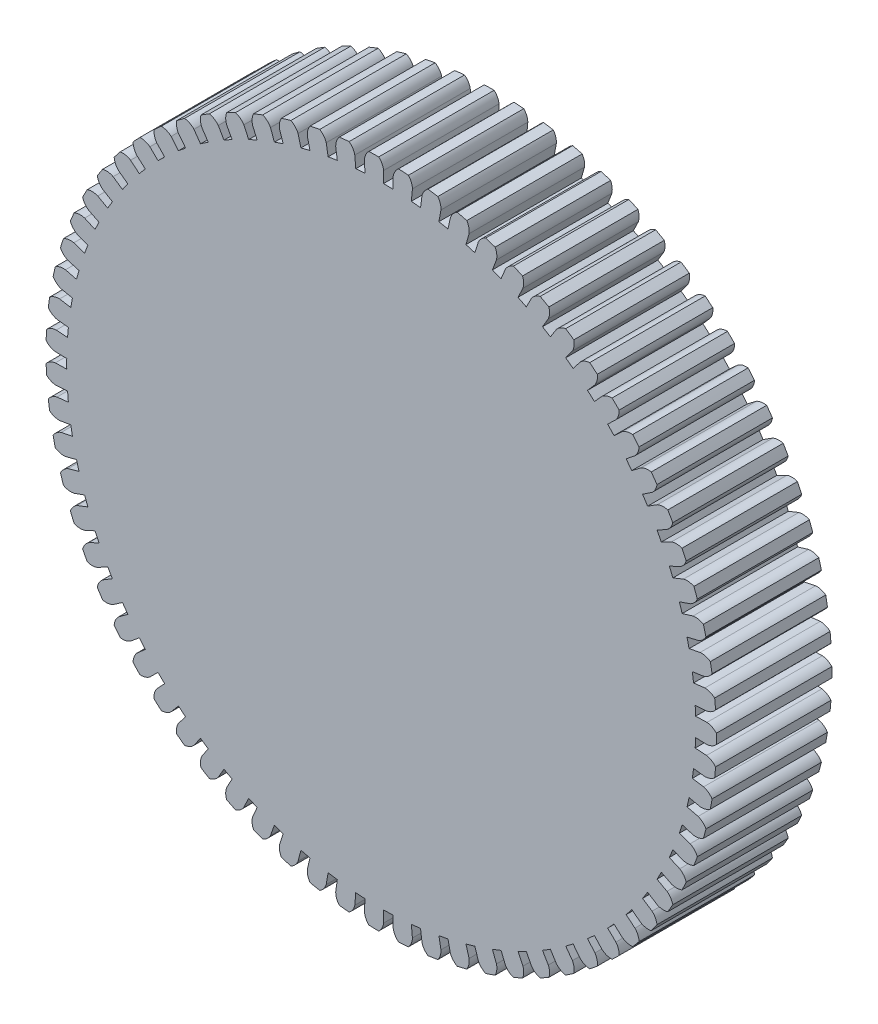
SolidWorks part; units mm, degrees
ref_plane "Front Plane" through (0, 0, 0) normal (0, 0, 1) x (1, 0, 0)
ref_plane "Top Plane" through (0, 0, 0) normal (0, 1, 0) x (1, 0, 0)
ref_plane "Right Plane" through (0, 0, 0) normal (1, 0, 0) x (0, 0, -1)
sketch "Sketch1" plane through (0, 0, 0) normal (0, 0, 1) x (1, 0, 0)
  line L1 (0, 0) -> (119.7826, 5.3036) construction
  line L3 (119.8478, 3.5364) -> (124.1959, 3.6647) construction
  line L4 (119.8478, 3.5364) -> (124.1959, 3.6647)
  line L5 (0, 0) -> (119.7826, 5.3036)
  line L6 (119.8478, -3.5364) -> (124.1959, -3.6647)
  line L7 (0, 0) -> (119.7826, -5.3036)
  arc A0 (127.7861, -1.8849) -> (127.7861, 1.8849) centre (0, 0) ccw construction
  arc A1 (119.8478, 3.5364) -> (119.7826, 5.3036) centre (0, 0) ccw construction
  arc A3 (127.7861, 1.8849) -> (127.7861, -1.8849) centre (0, 0) cw
  arc A4 (119.7826, 5.3036) -> (119.8478, 3.5364) centre (0, 0) cw
  arc A5 (124.1959, 3.6647) -> (127.7861, 1.8849) centre (123.6283, -1.9913) cw
  arc A6 (119.7826, -5.3036) -> (119.8478, -3.5364) centre (0, 0) ccw
  arc A7 (124.1959, -3.6647) -> (127.7861, -1.8849) centre (123.6283, 1.9913) ccw
  arc A8 (119.7826, -5.3036) -> (119.8478, -3.5364) centre (0, 0) ccw construction
  point P11 (119.8478, 3.5364)
  dimension "D1" = 239.8
  dimension "D3" = 255.6
  dimension "D7" = 5.6844
extrude "Boss-Extrude6" add sketch "Sketch1" along normal mid plane 44 contours L6 A7 A3 A5 L4 A4 L5 L7 A6
pattern_circular "CirPattern1" count 71 over 360 about axis through (0, 0, 0) along (0, 0, 1) of "Boss-Extrude6"
sketch "Sketch2" plane through (0, 0, 0) normal (0, 0, 1) x (1, 0, 0)
  circle A0 centre (0, 0) radius 124.25 construction
  dimension "D1" = 248.5
